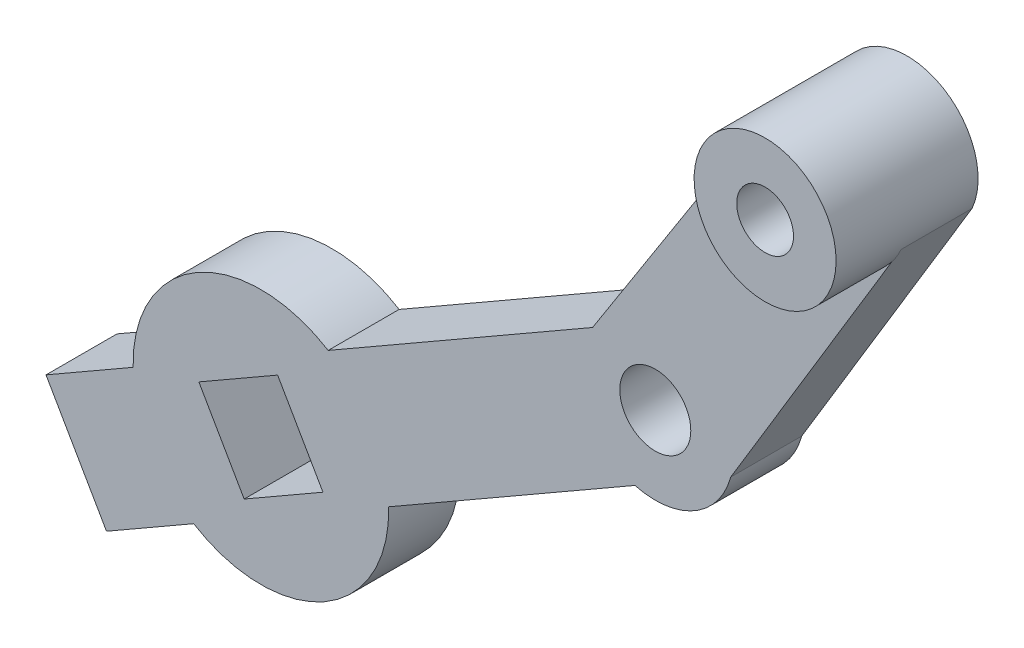
SolidWorks part; units mm, degrees
ref_plane "Front Plane" through (0, 0, 0) normal (0, 0, 1) x (1, 0, 0)
ref_plane "Top Plane" through (0, 0, 0) normal (0, 1, 0) x (1, 0, 0)
ref_plane "Right Plane" through (0, 0, 0) normal (1, 0, 0) x (0, 0, -1)
sketch "Sketch1" plane through (0, 0, 0) normal (0, 0, 1) x (0.4985, -0.8669, 0)
  line L0 (4.6263, -46.838) -> (4.6263, -41.838) construction
  line L2 (8.8991, 3.8691) -> (-2.3564, 24.18)
  line L3 (1.121, -3.909) -> (-10.421, 18.2671)
  line L4 (-2.3564, 24.18) -> (-10.421, 18.2671) construction
  line L6 (0.3536, -46.838) -> (8.8991, -46.838)
  line L7 (0.3536, -46.838) -> (0.3536, -2.4346)
  line L9 (8.8991, -46.838) -> (8.8991, -3.909)
  circle A0 centre (5.01, -0.02) radius 2.5
  arc A1 (1.121, -3.909) -> (8.8991, 3.8691) centre (5.01, -0.02) ccw
  arc A2 (-2.3564, 24.18) -> (-10.421, 18.2671) centre (-6.3887, 21.2235) ccw
  circle A3 centre (-6.3887, 21.2235) radius 2
  circle A5 centre (5.01, -0.02) radius 5.5 construction
  point P16 (10.01, -0.02)
  dimension "D2" = 4
  dimension "D3" = 5
  dimension "D5" = 5
  dimension "D4" = 25
  dimension "D6" = 42.929
  dimension "D7" = 8.5456
  dimension "D8" = 10
  dimension "D1" = 3
extrude "Boss-Extrude1" add sketch "Sketch1" along normal blind 5 contours L2 A2 L3 A1 A3 A0 | A1 L3 L7 L6 L9
sketch "Sketch3" plane through (0, 0, 0) normal (0, 0, -1) x (-1, 0, 0)
  line L0 (36.092, -21.164) -> (18.7546, -11.1934) construction
  line L1 (36.1662, -31.0645) -> (40.4264, -23.6566) construction
  line L2 (40.4264, -23.6566) -> (18.7546, -11.1934) construction
  line L3 (40.4264, -23.6566) -> (1.9342, -1.5202) construction
  line L4 (18.7546, -11.1934) -> (14.4943, -18.6013) construction
  line L5 (36.1662, -31.0645) -> (-1.0478, -9.6632) construction
  line L6 (14.4943, -18.6013) -> (36.1662, -31.0645) construction
  line L7 (36.1662, -31.0645) -> (40.4264, -23.6566)
  line L8 (36.1662, -31.0645) -> (31.8318, -28.5719)
  line L9 (40.4264, -23.6566) -> (36.092, -21.164)
  line L10 (31.8318, -28.5719) -> (36.092, -21.164)
  line L11 (14.4943, -18.6013) -> (18.7546, -11.1934)
  line L12 (14.4943, -18.6013) -> (10.16, -16.1087)
  line L13 (18.7546, -11.1934) -> (14.4202, -8.7007)
  line L14 (10.16, -16.1087) -> (14.4202, -8.7007)
  dimension "D1" = 20
  dimension "D2" = 5
  dimension "D3" = 5
sketch "Sketch4" plane through (0, 0, 5) normal (0, 0, 1) x (1, 0, 0)
  line L5 (10.6401, 18.1404) -> (-1.9342, -1.5202)
  line L6 (-1.9342, -1.5202) -> (-40.4264, -23.6566)
  line L7 (-40.4264, -23.6566) -> (-36.1662, -31.0645)
  line L8 (-36.1662, -31.0645) -> (1.0478, -9.6632)
  line L9 (7.7905, -5.7855) -> (19.7862, 14.0971)
  line L10 (10.6401, 18.1404) -> (-1.9342, -1.5202)
  line L11 (-1.9342, -1.5202) -> (-40.4264, -23.6566)
  line L12 (-40.4264, -23.6566) -> (-36.1662, -31.0645)
  line L13 (-36.1662, -31.0645) -> (1.0478, -9.6632)
  line L14 (7.7905, -5.7855) -> (19.7862, 14.0971)
  arc A2 (1.0478, -9.6632) -> (7.7905, -5.7855) centre (2.4803, -4.353) ccw
  arc A3 (19.7862, 14.0971) -> (10.6401, 18.1404) centre (15.2132, 16.1188) ccw
  arc A4 (1.0478, -9.6632) -> (7.7905, -5.7855) centre (2.4803, -4.353) ccw
  arc A5 (19.7862, 14.0971) -> (10.6401, 18.1404) centre (15.2132, 16.1188) ccw
  dimension "D1" = 0
ref_plane "Plane1" through (2.3064, -4.0104, 0) normal (0.4985, -0.8669, 0) x (0.8669, 0.4985, 0)
sketch "Sketch6" plane through (0, 0, 5) normal (0, 0, 1) x (1, 0, 0)
  line L0 (-38.2963, -27.3606) -> (-25.2932, -19.8826) construction
  line L5 (10.6401, 18.1404) -> (-1.9342, -1.5202)
  line L6 (-1.9342, -1.5202) -> (-40.4264, -23.6566)
  line L7 (-40.4264, -23.6566) -> (-36.1662, -31.0645)
  line L8 (-36.1662, -31.0645) -> (1.0478, -9.6632)
  line L9 (7.7905, -5.7855) -> (19.7862, 14.0971)
  line L10 (10.6401, 18.1404) -> (-1.9342, -1.5202)
  line L11 (-1.9342, -1.5202) -> (-40.4264, -23.6566)
  line L12 (-40.4264, -23.6566) -> (-36.1662, -31.0645)
  line L13 (-36.1662, -31.0645) -> (1.0478, -9.6632)
  line L14 (7.7905, -5.7855) -> (19.7862, 14.0971)
  circle A1 centre (-25.2932, -19.8826) radius 2.5 construction
  arc A2 (1.0478, -9.6632) -> (7.7905, -5.7855) centre (2.4803, -4.353) ccw
  arc A3 (19.7862, 14.0971) -> (10.6401, 18.1404) centre (15.2132, 16.1188) ccw
  arc A4 (1.0478, -9.6632) -> (7.7905, -5.7855) centre (2.4803, -4.353) ccw
  arc A5 (19.7862, 14.0971) -> (10.6401, 18.1404) centre (15.2132, 16.1188) ccw
  circle A6 centre (-25.2932, -19.8826) radius 9
  dimension "D3" = 5
  dimension "D4" = 18
  dimension "D2" = 15
  dimension "D1" = 0
extrude "Boss-Extrude3" add sketch "Sketch6" against normal up to surface (5 mm away) contours A6 up to face at (-5.2053, -5.1823, 0)
sketch "Sketch12" plane through (0, 0, 5) normal (0, 0, 1) x (1, 0, 0)
  line L0 (-20.9239, -21.0613) -> (-24.1145, -15.5133)
  line L1 (-20.9239, -21.0613) -> (-26.4719, -24.2519)
  line L2 (-24.1145, -15.5133) -> (-29.6625, -18.7039)
  line L3 (-26.4719, -24.2519) -> (-29.6625, -18.7039)
  line L4 (-20.9239, -21.0613) -> (-29.6625, -18.7039) construction
  line L5 (-24.1145, -15.5133) -> (-26.4719, -24.2519) construction
  line L6 (-40.4264, -23.6566) -> (-36.1662, -31.0645) construction
  point P1 (-25.2932, -19.8826)
  dimension "D1" = 6.4
  dimension "D2" = 6.4
extrude "Cut-Extrude1" cut sketch "Sketch12" against normal up to next
sketch "Sketch13" plane through (-24.8256, -14.2769, 0) normal (-0.8669, -0.4985, 0) x (0, 0, 1)
  line L0 (0, -4.6263) -> (5, -4.6263) construction
  line L1 (0, -1.4263) -> (0, -7.8263) construction
  line L2 (5, -7.8263) -> (5, -1.4263) construction
  circle A0 centre (2.5, -4.6263) radius 1
  dimension "D1" = 2
extrude "Cut-Extrude2" cut sketch "Sketch13" against normal blind 0.5
sketch "Sketch7" plane through (0, 0, 0) normal (0, 0, -1) x (-1, 0, 0)
  line L0 (25.2932, -19.8826) -> (38.2963, -27.3606) construction
  line L1 (20.3098, -19.4757) -> (30.2766, -20.2896)
  circle A0 centre (25.2932, -19.8826) radius 5 construction
  arc A1 (20.3098, -19.4757) -> (30.2766, -20.2896) centre (25.2932, -19.8826) cw
  dimension "D1" = 10
sketch "Sketch5" plane through (0, 0, 5) normal (0, 0, 1) x (1, 0, 0)
  line L4 (-18.7546, -11.1934) -> (-14.4943, -18.6013)
  line L5 (10.6401, 18.1404) -> (-1.9342, -1.5202)
  line L6 (-1.9342, -1.5202) -> (-20.5567, -12.2298)
  line L7 (-40.4264, -23.6566) -> (-36.1662, -31.0645)
  line L8 (-36.1662, -31.0645) -> (-30.0296, -27.5355)
  line L9 (7.7905, -5.7855) -> (19.7862, 14.0971)
  line L10 (10.6401, 18.1404) -> (-1.9342, -1.5202)
  line L11 (-1.9342, -1.5202) -> (-20.5567, -12.2298)
  line L12 (-40.4264, -23.6566) -> (-36.1662, -31.0645)
  line L13 (-36.1662, -31.0645) -> (-30.0296, -27.5355)
  line L14 (7.7905, -5.7855) -> (19.7862, 14.0971)
  line L15 (-14.4202, -8.7007) -> (-18.7546, -11.1934)
  line L16 (-10.16, -16.1087) -> (-14.4202, -8.7007)
  line L17 (-14.4943, -18.6013) -> (-10.16, -16.1087)
  line L18 (-18.7546, -11.1934) -> (-14.4943, -18.6013)
  line L19 (-14.4202, -8.7007) -> (-18.7546, -11.1934)
  line L20 (-10.16, -16.1087) -> (-14.4202, -8.7007)
  line L21 (-14.4943, -18.6013) -> (-10.16, -16.1087)
  line L22 (-40.4264, -23.6566) -> (-36.1662, -31.0645)
  line L23 (-36.092, -21.164) -> (-40.4264, -23.6566)
  line L24 (-31.8318, -28.5719) -> (-36.092, -21.164)
  line L25 (-36.1662, -31.0645) -> (-31.8318, -28.5719)
  line L26 (-40.4264, -23.6566) -> (-36.1662, -31.0645)
  line L27 (-36.092, -21.164) -> (-40.4264, -23.6566)
  line L28 (-31.8318, -28.5719) -> (-36.092, -21.164)
  line L29 (-36.1662, -31.0645) -> (-31.8318, -28.5719)
  line L33 (-16.2965, -19.6377) -> (1.0478, -9.6632)
  line L34 (-16.2965, -19.6377) -> (1.0478, -9.6632)
  line L35 (-34.2898, -20.1276) -> (-40.4264, -23.6566)
  line L36 (-34.2898, -20.1276) -> (-40.4264, -23.6566)
  arc A2 (1.0478, -9.6632) -> (7.7905, -5.7855) centre (2.4803, -4.353) ccw
  arc A3 (19.7862, 14.0971) -> (10.6401, 18.1404) centre (15.2132, 16.1188) ccw
  arc A4 (1.0478, -9.6632) -> (7.7905, -5.7855) centre (2.4803, -4.353) ccw
  arc A5 (19.7862, 14.0971) -> (10.6401, 18.1404) centre (15.2132, 16.1188) ccw
  arc A8 (-30.0296, -27.5355) -> (-16.2965, -19.6377) centre (-25.2932, -19.8826) ccw
  arc A9 (-30.0296, -27.5355) -> (-16.2965, -19.6377) centre (-25.2932, -19.8826) ccw
  arc A10 (-20.5567, -12.2298) -> (-34.2898, -20.1276) centre (-25.2932, -19.8826) ccw
  arc A11 (-20.5567, -12.2298) -> (-34.2898, -20.1276) centre (-25.2932, -19.8826) ccw
  dimension "D1" = 0
  dimension "D2" = 0
  dimension "D3" = 0
sketch "Sketch9" plane through (0, 0, 5) normal (0, 0, 1) x (1, 0, 0)
  circle A0 centre (15.2132, 16.1188) radius 2
  circle A1 centre (2.4803, -4.353) radius 2.5
sketch "Sketch14" plane through (0, 0, 5) normal (0, 0, 1) x (1, 0, 0)
  circle A0 centre (15.2132, 16.1188) radius 2
  circle A1 centre (15.2132, 16.1188) radius 5
extrude "Boss-Extrude4" add sketch "Sketch14" along normal blind 5
